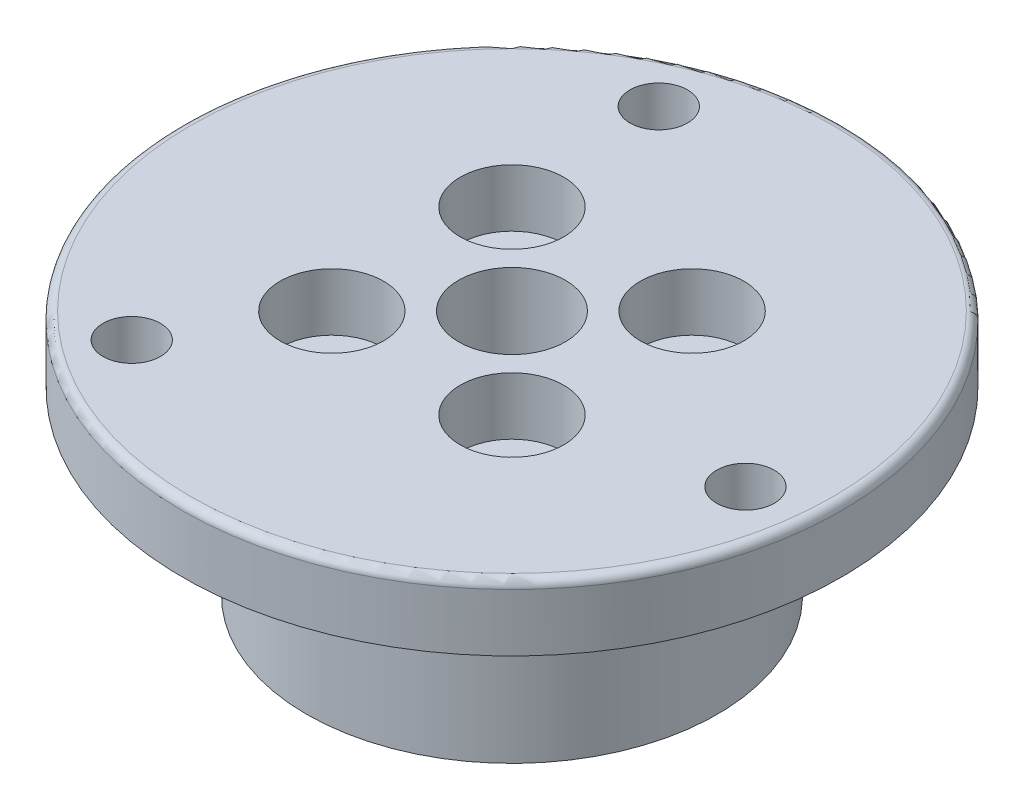
SolidWorks part; units mm, degrees
ref_plane "前基準面" through (0, 0, 0) normal (0, 0, 1) x (1, 0, 0)
ref_plane "上基準面" through (0, 0, 0) normal (0, 1, 0) x (1, 0, 0)
ref_plane "右基準面" through (0, 0, 0) normal (1, 0, 0) x (0, 0, -1)
sketch "Sketch1" plane through (0, 0, 0) normal (0, 1, 0) x (1, 0, 0)
  line L0 (0, 0) -> (-6.3143, 15.244) construction
  line L5 (-5.4801, 5.4801) -> (-5.4801, -5.4801) construction
  line L7 (0, 0) -> (0, 21.4212) construction
  circle A1 centre (0, 0) radius 3.25
  circle A2 centre (5.4801, 5.4801) radius 1.75
  circle A3 centre (5.4801, -5.4801) radius 1.75
  circle A4 centre (-5.4801, -5.4801) radius 1.75
  circle A5 centre (-5.4801, 5.4801) radius 1.75
  circle A6 centre (-10.0446, -13.0903) radius 1.75
  circle A7 centre (-6.3143, 15.244) radius 1.75
  circle A8 centre (16.3588, -2.1537) radius 1.75
  circle A9 centre (0, 0) radius 20.05
  point P15 (0, 0)
  point P25 (0, 0)
  dimension "D2" = 6.5
  dimension "D5" = 3.5
  dimension "D8" = 3.5
  dimension "D11" = 40.1
  dimension "D4" = 15.5
  dimension "D6" = 22.5
  dimension "D10" = 16.5
  dimension "D3" = 4
  dimension "D9" = 3
extrude "Extrude1" add sketch "Sketch1" along normal blind 15
sketch "Sketch7" plane through (0, 15, 0) normal (0, 1, 0) x (1, 0, 0)
  circle A0 centre (-5.4801, 5.4801) radius 3.15
  circle A1 centre (5.4801, 5.4801) radius 3.15
  circle A2 centre (5.4801, -5.4801) radius 3.15
  circle A3 centre (-5.4801, -5.4801) radius 3.15
  dimension "D1" = 6.3
extrude "Extrude4" cut sketch "Sketch7" against normal blind 3.5
sketch "Sketch8" plane through (0, 0, 0) normal (0, -1, 0) x (1, 0, 0)
  circle A0 centre (0, 0) radius 20.05
  circle A1 centre (0, 0) radius 12.5
  dimension "D1" = 25
extrude "Extrude5" cut sketch "Sketch8" against normal blind 11
fillet "圓角1" radius 0.5 1 edges at (0, 15, 20.05)
